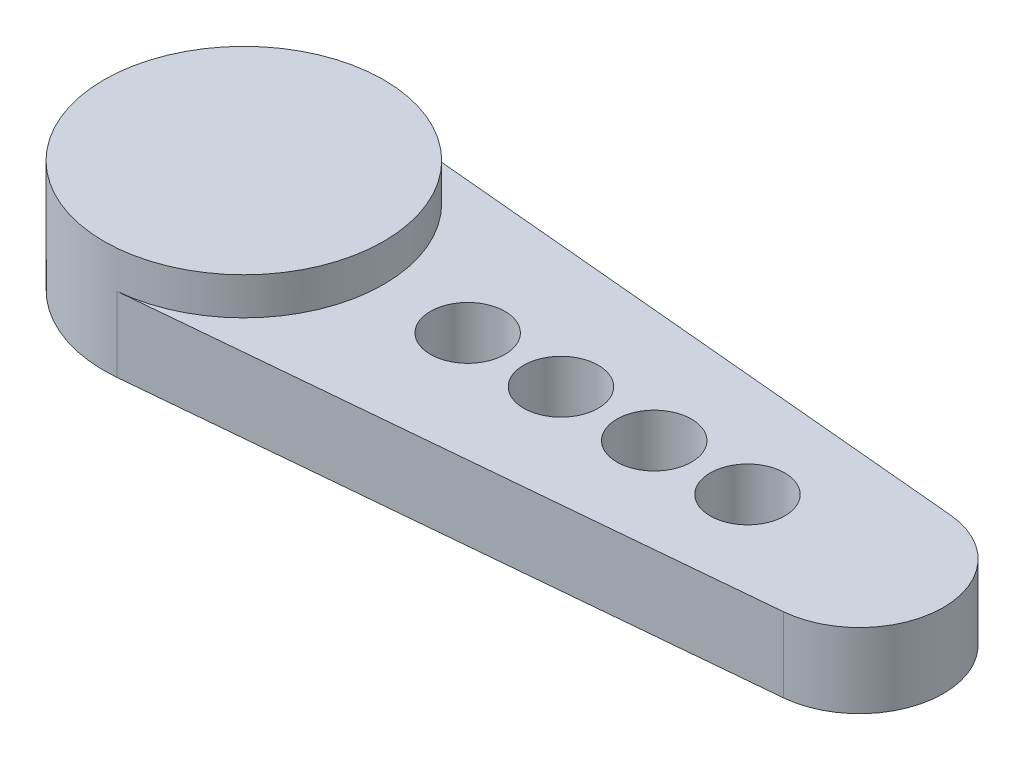
SolidWorks part; units mm, degrees
ref_plane "Front Plane" through (0, 0, 0) normal (0, 0, 1) x (1, 0, 0)
ref_plane "Top Plane" through (0, 0, 0) normal (0, 1, 0) x (1, 0, 0)
ref_plane "Right Plane" through (0, 0, 0) normal (1, 0, 0) x (0, 0, -1)
sketch "Sketch1" plane through (0, 0, 0) normal (0, 1, 0) x (1, 0, 0)
  line L0 (0, 0) -> (6, 0) construction
  line L1 (0.3409, 3.7345) -> (16.7045, 2.2407)
  line L2 (0.3409, -3.7345) -> (16.7045, -2.2407)
  line L3 (6, 0) -> (8.5, 0) construction
  line L4 (8.5, 0) -> (11, 0) construction
  line L5 (11, 0) -> (13.5, 0) construction
  line L6 (13.5, 0) -> (16.5, 0) construction
  arc A0 (0.3409, 3.7345) -> (0.3409, -3.7345) centre (0, 0) ccw
  arc A1 (16.7045, -2.2407) -> (16.7045, 2.2407) centre (16.5, 0) ccw
  circle A2 centre (6, 0) radius 1
  circle A3 centre (8.5, 0) radius 1
  circle A4 centre (11, 0) radius 1
  circle A5 centre (13.5, 0) radius 1
  dimension "D1" = 7.5
  dimension "D2" = 4.5
  dimension "D4" = 6
  dimension "D8" = 2
  dimension "D3" = 16.5
  dimension "D5" = 2.5
  dimension "D6" = 2.5
  dimension "D7" = 2.5
extrude "Boss-Extrude1" add sketch "Sketch1" along normal blind 2
sketch "Sketch2" plane through (0, 2, 0) normal (0, 1, 0) x (1, 0, 0)
  circle A0 centre (0, 0) radius 3.75
extrude "Boss-Extrude2" add sketch "Sketch2" along normal blind 1
sketch "Sketch3" plane through (0, 0, 0) normal (0, -1, 0) x (1, 0, 0)
  circle A0 centre (0, 0) radius 2.75
  dimension "D1" = 5.5
extrude "Cut-Extrude1" cut sketch "Sketch3" against normal blind 1
